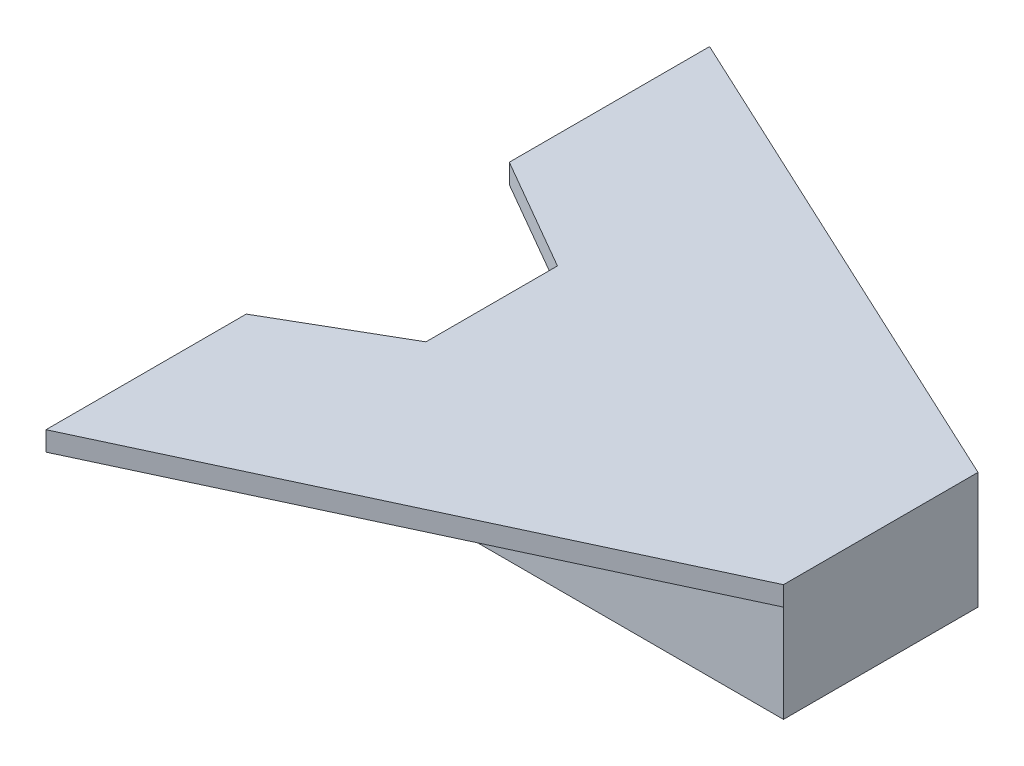
SolidWorks part; units mm, degrees
ref_plane "Front Plane" through (0, 0, 0) normal (0, 0, 1) x (1, 0, 0)
ref_plane "Top Plane" through (0, 0, 0) normal (0, 1, 0) x (1, 0, 0)
ref_plane "Right Plane" through (0, 0, 0) normal (1, 0, 0) x (0, 0, -1)
sketch "Sketch1" plane through (0, 0, 0) normal (0, 1, 0) x (1, 0, 0)
  line L0 (0, 500) -> (-1292.7596, 1102.8237)
  line L1 (0, 0) -> (-1000, 0)
  line L2 (0, 0) -> (0, 500)
  line L3 (0, 500) -> (-1000, 500)
  line L4 (-1000, 0) -> (-1000, 500)
  line L5 (-1292.7596, 1102.8237) -> (-1292.7596, 588.0497)
  line L6 (0, 250) -> (-1000, 250) construction
  line L7 (0, 0) -> (-1000, 0)
  line L11 (-1292.7596, -88.0497) -> (-1000, 80.9752)
  line L12 (-1000, 80.9752) -> (-1000, 419.0248)
  line L13 (-1000, 419.0248) -> (-1292.7596, 588.0497)
  line L14 (0, 0) -> (-1292.7596, -602.8237)
  line L15 (-1292.7596, -88.0497) -> (-1292.7596, -602.8237)
  line L16 (-1585.5192, 250) -> (-1585.5192, 80.9752) [skipped]
  line L17 (-1439.1394, -3.5373) -> (-1292.7596, -88.0497) [skipped]
  line L18 (-1292.7596, 588.0497) -> (-1439.1394, 503.5373) [skipped]
  dimension "D1" = 500
  dimension "D2" = 25
  dimension "D3" = 1000
  dimension "D4" = 0
extrude "Boss-Extrude1" add sketch "Sketch1" along normal blind 50 contours L13 L4 L3 L0 L5 | L6 L2 L3 L4 L12 | L2 L6 L4 L1 | L11 L15 L14 L1 L4
sketch "Sketch2" plane through (0, 0, 0) normal (0, -1, 0) x (1, 0, 0)
  line L0 (-1000, -80.9752) -> (-1000, -419.0248) construction
  line L1 (0, 0) -> (-950, 0)
  line L2 (0, 0) -> (0, -500)
  line L3 (0, -500) -> (-950, -500)
  line L4 (-950, 0) -> (-950, -500)
  dimension "D1" = 50
extrude "Boss-Extrude2" add sketch "Sketch2" along normal blind 250
sketch "Sketch3" plane through (0, 0, 0) normal (0, 0, 1) x (1, 0, 0)
  line L0 (-950, -250) -> (-950, 0) construction
  line L1 (0, -250) -> (-950, -250) construction
  circle A0 centre (-700, -170) radius 5
  dimension "D1" = 10
  dimension "D2" = 250
  dimension "D3" = 80
extrude "Cut-Extrude1" cut sketch "Sketch3" against normal up to surface (500 mm away) up to face at (-475, -125, -500)
sketch "Sketch4" plane through (-950, 0, 0) normal (-1, 0, 0) x (0, 0, 1)
  text T0 "2FST-4U" font "Century Gothic" height 30
extrude "Boss-Extrude3" add sketch "Sketch4" along normal blind 3
